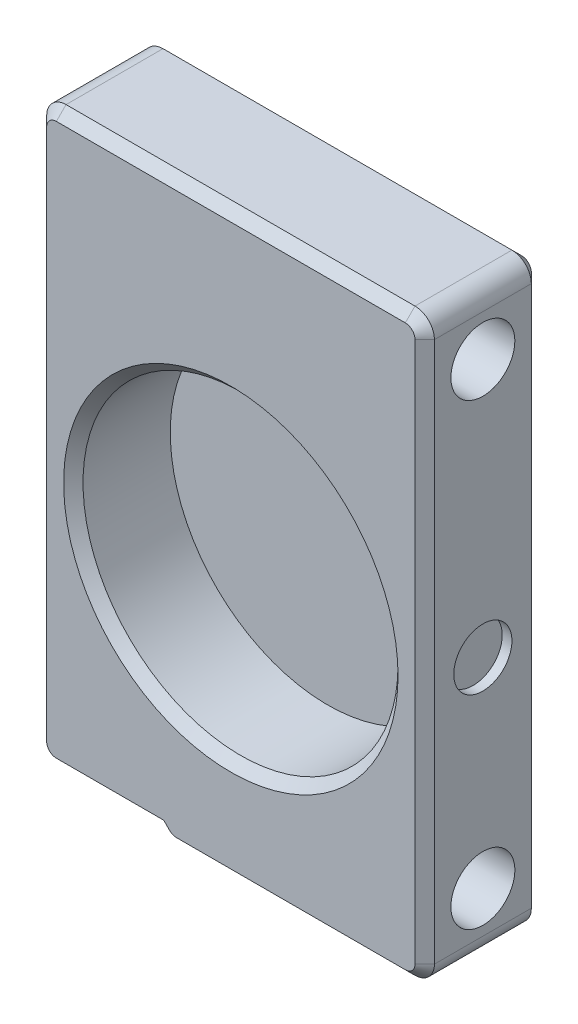
SolidWorks part; units mm, degrees
ref_plane "Front Plane" through (0, 0, 0) normal (0, 0, 1) x (1, 0, 0)
ref_plane "Top Plane" through (0, 0, 0) normal (0, 1, 0) x (1, 0, 0)
ref_plane "Right Plane" through (0, 0, 0) normal (1, 0, 0) x (0, 0, -1)
sketch "Sketch1" plane through (0, 0, 0) normal (0, 0, 1) x (1, 0, 0)
  line L0 (-10, 8.165) -> (10, 8.165) construction
  line L1 (-3.17, -13.5) -> (10, -13.5)
  line L2 (-10, -13) -> (-10, 13.5)
  line L3 (-10, 13.5) -> (10, 13.5) construction
  line L4 (10, -13.5) -> (10, 13.5)
  line L5 (-10, -13.5) -> (10, 13.5) construction
  line L6 (-10, 13.5) -> (10, -13.5) construction
  line L7 (10, 11.765) -> (-10, 11.765) construction
  line L8 (-10, -13) -> (-3.67, -13)
  line L9 (-3.67, -13) -> (-3.17, -13.5)
  line L10 (-10, 13.5) -> (-10, 16.5)
  line L11 (-10, 16.5) -> (10, 16.5)
  line L12 (-10, -13.5) -> (-3.17, -13.5) construction
  line L13 (-10, -13.5) -> (-10, -13) construction
  line L14 (10, 16.5) -> (10, 13.5)
  circle A0 centre (0, 0) radius 8 construction
  point P0 (0, 0)
  dimension "D3" = 16
  dimension "D4" = 3.6
  dimension "D1" = 20
  dimension "D2" = 27
  dimension "D5" = 3
  dimension "D6" = 0.5
  dimension "D7" = 45
extrude "Boss-Extrude1" add sketch "Sketch1" along normal blind 6
sketch "Sketch2" plane through (0, 0, 6) normal (0, 0, 1) x (1, 0, 0)
  circle A0 centre (0, 0) radius 8.125
  dimension "D1" = 16.25
extrude "Cut-Extrude1" cut sketch "Sketch2" against normal blind 5
sketch "Sketch3" plane through (10, 0, 0) normal (1, 0, 0) x (0, 0, -1)
  line L0 (0, 0) -> (-6, 0) construction
  line L2 (-6, -13.5) -> (-6, 16.5) construction
  circle A0 centre (-3, 0) radius 1.5
  dimension "D1" = 3
extrude "Cut-Extrude2" cut sketch "Sketch3" against normal blind 0.5
sketch "Sketch4" plane through (10, 0, 0) normal (1, 0, 0) x (0, 0, -1)
  line L0 (-3, 16.5) -> (-3, 0) construction
  line L2 (-3, 0) -> (0, 0) construction
  line L3 (-6, -13.5) -> (0, -13.5) construction
  line L4 (-6, 16.5) -> (0, 16.5) construction
  circle A0 centre (-3, 13.32) radius 1.65
  circle A1 centre (-3, -10.3154) radius 1.65
  dimension "D1" = 3.3
  dimension "D2" = 3.1846
  dimension "D3" = 3.18
extrude "Cut-Extrude3" cut sketch "Sketch4" against normal through all
sketch "Sketch5" plane through (0, 0, 0) normal (0, 0, -1) x (-1, 0, 0)
  line L0 (-10, 1.5) -> (10, 1.5) construction
  line L1 (-10, 16.5) -> (-10, 16.45)
  line L2 (-10, -13.5) -> (-10, 16.5) construction
  line L3 (-10, 16.45) -> (10, 16.45)
  line L4 (10, 16.5) -> (10, -13) construction
  line L5 (10, 16.45) -> (10, 16.5)
  line L6 (10, 16.5) -> (-10, 16.5)
  line L7 (10, -13.5) -> (-10, -13.5)
  line L8 (10, -13.45) -> (10, -13.5)
  line L9 (-10, -13.45) -> (10, -13.45)
  line L10 (-10, -13.5) -> (-10, -13.45)
  dimension "D1" = 0.05
extrude "Cut-Extrude4" cut sketch "Sketch5" against normal through all
fillet "Fillet1" radius 1 5 edges at (-10, -13, 3) (-3.22, -13.45, 3) (10, -13.45, 3) (-10, 16.45, 3) (10, 16.45, 3)
chamfer "Chamfer1" distance 0.5 angle 45 23 edges at (8.125, 0, 6) (-10, 1.725, 0) (10, 1.5, 0) (-10, 1.725, 6) (10, 1.5, 6) (-6.335, -13, 0) (-3.5915, -13.0786, 0) (-3.5915, -13.0786, 6) (-6.335, -13, 6) (-9.7071, -12.7071, 0) (-9.7071, -12.7071, 6) (3.0971, -13.45, 0) (0, 16.45, 0) (0, 16.45, 6) (3.0971, -13.45, 6) (9.7071, -13.1571, 0) (9.7071, 16.1571, 0) (-9.7071, 16.1571, 0) (-3.1885, -13.3739, 0) (-9.7071, 16.1571, 6) (9.7071, 16.1571, 6) (9.7071, -13.1571, 6) (-3.1885, -13.3739, 6)
